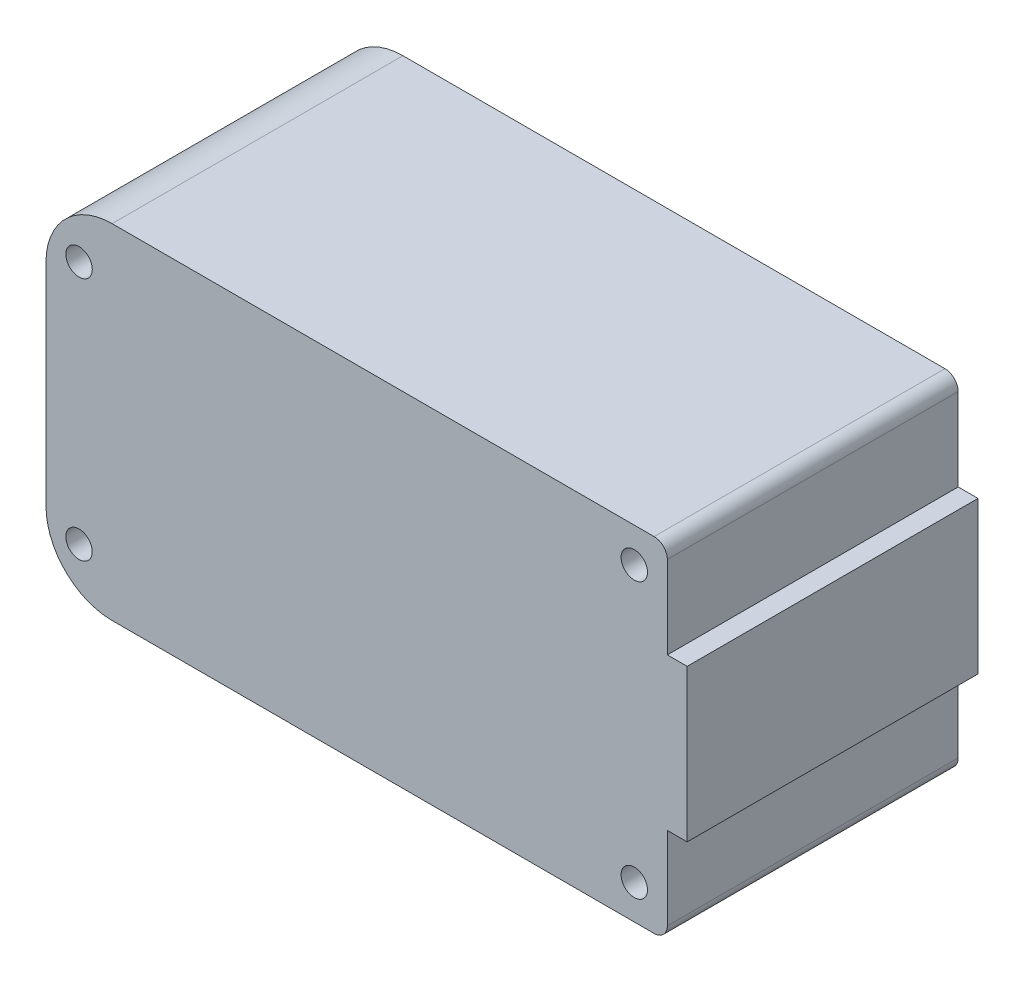
SolidWorks part; units mm, degrees
ref_plane "Front" through (0, 0, 0) normal (0, 0, 1) x (1, 0, 0)
ref_plane "Top" through (0, 0, 0) normal (0, 1, 0) x (1, 0, 0)
ref_plane "Right" through (0, 0, 0) normal (1, 0, 0) x (0, 0, -1)
sketch "Sketch1" plane through (0, 0, 0) normal (0, 0, 1) x (1, 0, 0)
  line L0 (12, 0) -> (37, 0) construction
  line L1 (35.5, -13) -> (-11.5, -13)
  line L2 (35.5, -13) -> (35.5, -5.75)
  line L3 (35.5, 13) -> (-11.5, 13)
  line L4 (-11.5, -13) -> (-11.5, 13)
  line L5 (35.5, -13) -> (-11.5, 13) construction
  line L6 (35.5, 13) -> (-11.5, -13) construction
  line L10 (35.5, 5.75) -> (35.5, 13)
  line L11 (35.5, 5.75) -> (37, 5.75)
  line L12 (35.5, -5.75) -> (37, -5.75)
  line L13 (37, 5.75) -> (37, -5.75)
  circle A0 centre (-9, 9.25) radius 1
  circle A1 centre (33, 10.4) radius 1
  circle A2 centre (33, -10.4) radius 1
  circle A3 centre (-9, -9.25) radius 1
  point P0 (12, 0)
extrude "Boss-Extrude1" add sketch "Sketch1" along normal mid plane 22
fillet "Fillet1" radius 5 2 edges at (-11.5, 13, 0) (-11.5, -13, 0)
fillet "Fillet2" radius 1 2 edges at (35.5, 13, 0) (35.5, -13, 0)
